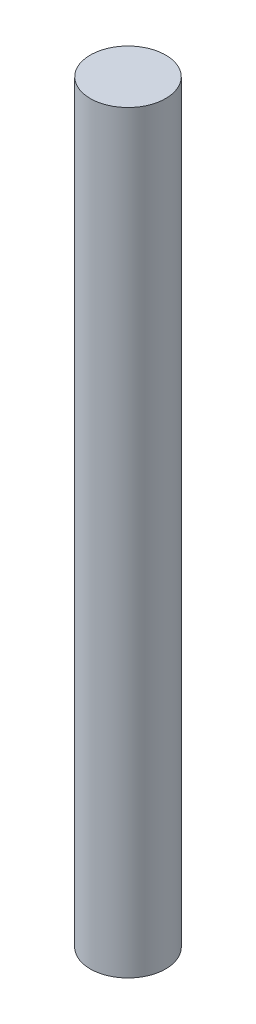
SolidWorks part; units mm, degrees
ref_plane "Front Plane" through (0, 0, 0) normal (0, 0, 1) x (1, 0, 0)
ref_plane "Top Plane" through (0, 0, 0) normal (0, 1, 0) x (1, 0, 0)
ref_plane "Right Plane" through (0, 0, 0) normal (1, 0, 0) x (0, 0, -1)
sketch "Sketch1" plane through (0, 0, 0) normal (0, 1, 0) x (1, 0, 0)
  circle A0 centre (0, 0) radius 10
extrude "Boss-Extrude1" add sketch "Sketch1" along normal blind 200
